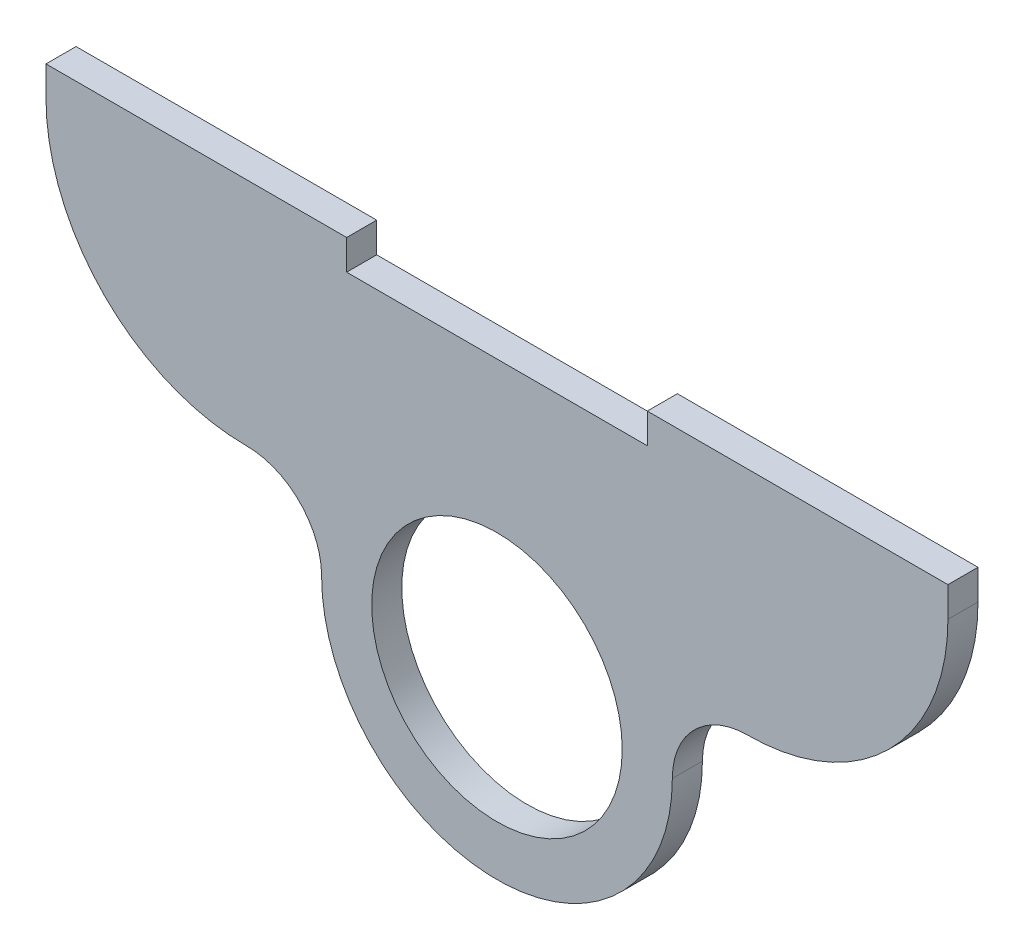
SolidWorks part; units mm, degrees
ref_plane "Front Plane" through (0, 0, 0) normal (0, 0, 1) x (1, 0, 0)
ref_plane "Top Plane" through (0, 0, 0) normal (0, 1, 0) x (1, 0, 0)
ref_plane "Right Plane" through (0, 0, 0) normal (1, 0, 0) x (0, 0, -1)
sketch "Sketch1" plane through (0, 0, 0) normal (0, 0, 1) x (1, 0, 0)
  line L0 (-8.5, 0) -> (8.5, 0) construction
  line L1 (-15, 27.5) -> (15, 27.5)
  line L2 (-45, 27.5) -> (-45, 28.6955) construction
  line L3 (45, 27.5) -> (45, 30.5) construction
  line L4 (-25, 7.5) -> (-49.9345, 7.5) construction
  line L5 (25, 7.5) -> (47.5049, 7.5) construction
  line L8 (-45, 27.5) -> (-45, 30.5)
  line L9 (-45, 30.5) -> (-15, 30.5)
  line L10 (-15, 27.5) -> (-15, 30.5)
  line L12 (45, 27.5) -> (45, 30.5)
  line L13 (45, 30.5) -> (15, 30.5)
  line L14 (15, 27.5) -> (15, 30.5)
  circle A0 centre (-8.5, 0) radius 1.5 construction
  circle A1 centre (8.5, 0) radius 1.5 construction
  circle A2 centre (0, 0) radius 3.5 construction
  circle A3 centre (0, 0) radius 12.5
  arc A4 (-17.5, 0) -> (17.5, 0) centre (0, 0) ccw
  arc A5 (-45, 27.5) -> (-25, 7.5) centre (-25, 27.5) ccw
  arc A6 (-17.5, 0) -> (-25, 7.5) centre (-25, 0) ccw
  arc A7 (17.5, 0) -> (25, 7.5) centre (25, 0) cw
  arc A8 (25, 7.5) -> (45, 27.5) centre (25, 27.5) ccw
  point P4 (0, 0)
  point P10 (0, 27.5)
  point P12 (0, 12.5)
  dimension "D1" = 3
  dimension "D3" = 7
  dimension "D5" = 25
  dimension "D9" = 5
  dimension "D2" = 17
  dimension "D4" = 90
  dimension "D6" = 15
  dimension "D7" = 20
  dimension "D8" = 3
extrude "Boss-Extrude1" add sketch "Sketch1" along normal blind 3
